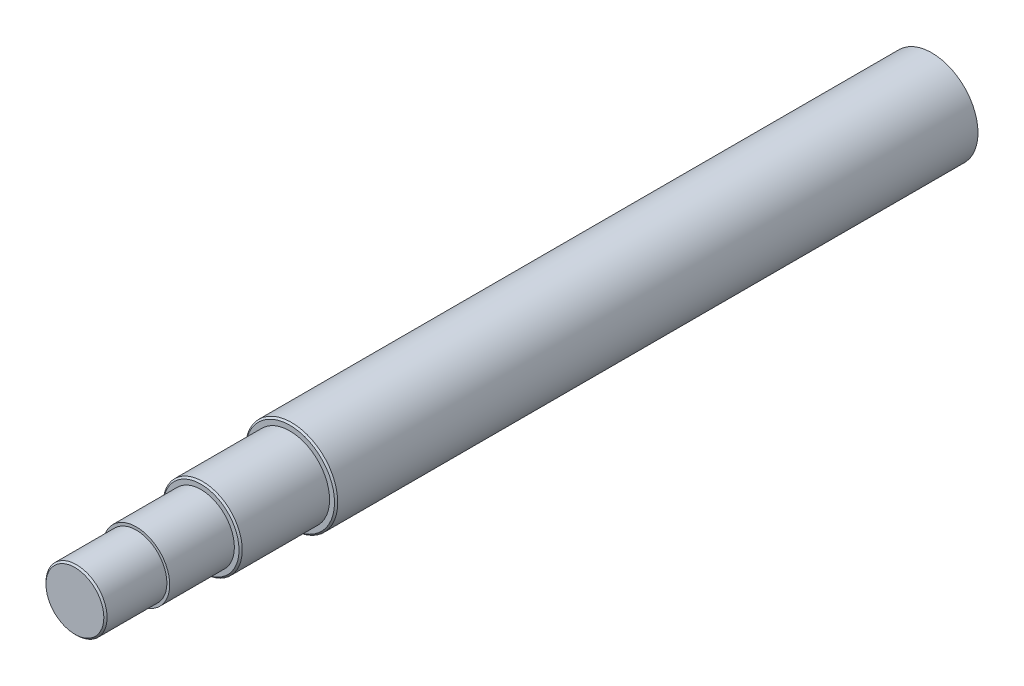
SolidWorks part; units mm, degrees
ref_plane "Front Plane" through (0, 0, 0) normal (0, 0, 1) x (1, 0, 0)
ref_plane "Top Plane" through (0, 0, 0) normal (0, 1, 0) x (1, 0, 0)
ref_plane "Right Plane" through (0, 0, 0) normal (1, 0, 0) x (0, 0, -1)
sketch "Sketch1" plane through (0, 0, 0) normal (0, 0, 1) x (1, 0, 0)
  circle A0 centre (0, 0) radius 28.575
  dimension "D1" = 57.15
extrude "Boss-Extrude1" add sketch "Sketch1" along normal blind 530
sketch "Sketch2" plane through (0, 0, 530) normal (0, 0, 1) x (1, 0, 0)
  circle A0 centre (0, 0) radius 18.9
  dimension "D1" = 37.8
extrude "Cut-Extrude1" cut sketch "Sketch2" against normal blind 38 flip side to cut
sketch "Sketch3" plane through (0, 0, 492) normal (0, 0, 1) x (1, 0, 0)
  circle A0 centre (0, 0) radius 20.64
  dimension "D1" = 41.28
extrude "Cut-Extrude2" cut sketch "Sketch3" against normal blind 40 flip side to cut
sketch "Sketch4" plane through (0, 0, 452) normal (0, 0, 1) x (1, 0, 0)
  circle A0 centre (0, 0) radius 24.5
  dimension "D1" = 49
extrude "Cut-Extrude3" cut sketch "Sketch4" against normal blind 55 flip side to cut
sketch "Sketch5" plane through (0, 0, 0) normal (0, 0, -1) x (-1, 0, 0)
  circle A0 centre (0, 0) radius 5
  dimension "D1" = 10
extrude "Boss-Extrude2" add sketch "Sketch5" along normal blind 5
chamfer "Chamfer1" distance 1 angle 45 3 edges at (28.575, 0, 397) (24.5, 0, 452) (18.9, 0, 530)
